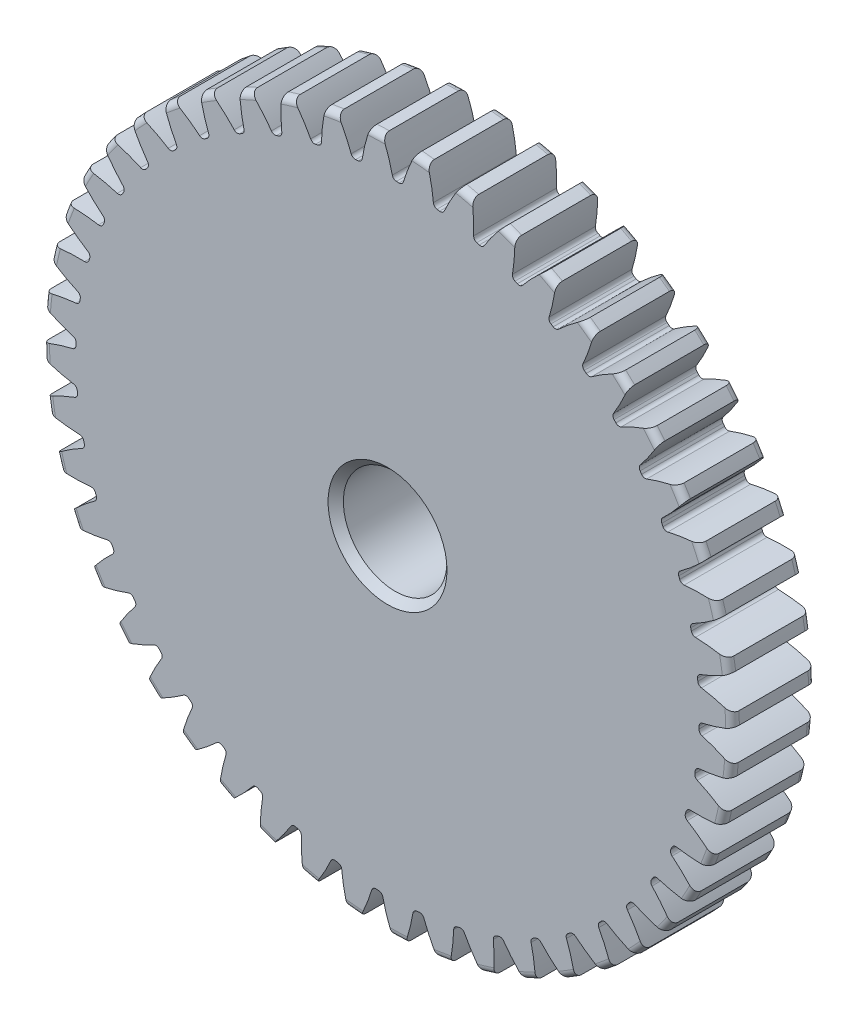
SolidWorks part; units mm, degrees
ref_plane "Front" through (0, 0, 0) normal (0, 0, 1) x (1, 0, 0)
ref_plane "Top" through (0, 0, 0) normal (0, 1, 0) x (1, 0, 0)
ref_plane "Right" through (0, 0, 0) normal (1, 0, 0) x (0, 0, -1)
sketch "Sketch1" plane through (0, 0, 0) normal (0, 0, 1) x (1, 0, 0)
  line L0 (-609.6, 0) -> (609.6, 0) construction
  circle A0 centre (0, 0) radius 26.416
  circle A1 centre (0, 0) radius 25.4 construction
  circle A3 centre (0, 0) radius 24.1755 construction
  dimension "D1" = 1.2245
  dimension "D2" = 2.2405
  dimension "D3" = 1.016
extrude "Boss-Extrude1" add sketch "Sketch1" against normal blind 6.35
sketch "Sketch2" plane through (0, 0, 0) normal (1, 0, 0) x (0, 0, -1)
  line L0 (6.35, 0) -> (14.224, 0)
  line L1 (6.35, 0) -> (6.35, 11.7078)
  line L2 (6.35, 11.7078) -> (14.224, 11.7078)
  line L3 (14.224, 11.7078) -> (14.224, 0)
  point P5 (14.224, -11.7078)
  point P6 (0, -26.416)
  point P7 (6.35, -26.416)
  point P9 (0, 26.416)
revolve "Revolve1" add sketch "Sketch2" angle 360 mid plane about L0
fillet "Fillet2" radius 0.5283 3 edges at (26.416, 0, -6.35) (26.416, 0, 0) (11.7078, 0, -6.35)
sketch "Sketch3" plane through (0, 0, 0) normal (0, 0, 1) x (1, 0, 0)
  line L0 (0, 0) -> (0, 26.416) construction
  line L1 (-8.1634, 22.4288) -> (0, 25.4)
  line L2 (-9.5921, 25.4) -> (9.5921, 25.4) construction
  line L3 (-9.0136, 22.1193) -> (9.0136, 28.6807) construction
  line L4 (-8.1634, 22.4288) -> (0, 0) construction
  line L5 (-19.9021, 13.1757) -> (0, 0) construction
  line L6 (-19.9021, 13.1757) -> (-6.7143, 33.096) construction
  line L7 (-5.6706, 23.1848) -> (0, 0) construction
  line L8 (-5.6706, 23.1848) -> (0.2364, 24.6296) construction
  arc A0 (-8.1634, 22.4288) -> (-19.9021, 13.1757) centre (0, 0) ccw
  circle A1 centre (0, 0) radius 25.4 construction
  circle A2 centre (0, 0) radius 23.8682 construction
  arc A3 (-8.1634, 22.4288) -> (-5.6706, 23.1848) centre (0, 0) cw
  circle A4 centre (0, 0) radius 26.416 construction
  point P6 (0, 25.4)
  dimension "D1" = 8.6873
  dimension "D3" = 23.8901
  dimension "D5" = 6.0811
  dimension "D2" = 15.2028
  dimension "D4" = 2.6062
sketch "Sketch4" plane through (0, 0, 0) normal (0, 0, 1) x (1, 0, 0)
  line L0 (0, 0) -> (0.8306, 25.3728) construction
  line L2 (0, 25.4) -> (1.6612, 25.3456) construction
  line L4 (0.4216, 23.8645) -> (0, 0) construction
  line L6 (-19.9021, 13.1757) -> (-6.7143, 33.096) construction
  line L7 (-19.9021, 13.1757) -> (-6.7143, 33.096) construction
  arc A0 (1.1401, 23.8409) -> (0.4216, 23.8645) centre (0, 0) ccw
  arc A1 (0, 25.4) -> (1.6612, 25.3456) centre (0, 0) cw construction
  circle A2 centre (0, 0) radius 25.4 construction
  circle A3 centre (0, 0) radius 23.8682 construction
  arc A5 (8.8645, 32.586) -> (-6.7143, 33.096) centre (0, 0) ccw
  spline S0 degree 2 poles (-6.7143, 33.096) (-0.803, 29.6485) (0.4216, 23.8645) knots 0 0 0 1 1 1
  spline S1 degree 2 poles (8.8645, 32.586) (2.7403, 29.5325) (1.1401, 23.8409) knots 0 0 0 1 1 1
  dimension "D1" = 1.6624
extrude "Cut-Extrude1" cut sketch "Sketch4" against normal through all
fillet "Fillet1" radius 0.3325 2 edges at (1.1401, 23.8409, -3.175) (0.4216, 23.8645, -3.175)
pattern_circular "CirPattern1" count 48 over 360 about axis through (0, 0, -6.35) along (0, 0, 1) of "Cut-Extrude1", "Fillet1"
sketch "Sketch5" plane through (0, 0, 0) normal (0, 0, 1) x (1, 0, 0)
  circle A0 centre (0, 0) radius 3.9688
  circle A1 centre (0, 0) radius 3.9688 construction
  dimension "Bore Min" = 7.9375
  dimension "Bore Max" = 7.9375
extrude "Cut-Extrude2" cut sketch "Sketch5" against normal through all
chamfer "Chamfer1" distance 0.5854 angle 45 3 edges at (11.7078, 0, -14.224) (3.9688, 0, 0) (3.9688, 0, -14.224)
sketch "Pitch Dia" plane through (0, 0, 0) normal (0, 0, 1) x (1, 0, 0)
  circle A0 centre (0, 0) radius 25.4 construction
  circle A1 centre (0, 0) radius 25.4 construction
sketch "Sketch6" plane through (0, 0, 0) normal (0, 0, 1) x (1, 0, 0)
  line L0 (-1.3337, 26.3823) -> (-0.3947, 26.4131)
  line L1 (-0.8642, 26.3977) -> (-0.7719, 23.5785) construction
  arc A0 (-2.2394, 23.7629) -> (-1.9424, 24.0403) centre (-2.2706, 24.0939) ccw construction
  arc A1 (-2.2394, 23.7629) -> (-2.4396, 23.7432) centre (0, 0) ccw construction
  arc A2 (0.366, 24.1159) -> (0.6804, 23.8585) centre (0.6899, 24.1908) ccw construction
  arc A3 (0.8815, 23.8519) -> (0.6804, 23.8585) centre (0, 0) ccw construction
  circle A4 centre (0, 0) radius 26.416 construction
  parabola Q2 (-1.5162, 25.8432) -> (-1.3337, 26.3823) focus (4.6524, 24.5229) apex (-1.1149, 26.9412) construction
  parabola Q3 (-1.9424, 24.0403) -> (-1.5162, 25.8432) focus (4.6524, 24.5229) apex (-1.1149, 26.9412) construction
  parabola Q4 (-1.9424, 24.0403) -> (-1.5162, 25.8432) focus (4.6524, 24.5229) apex (-1.1149, 26.9412) construction
  parabola Q5 (-1.9424, 24.0403) -> (-1.5162, 25.8432) focus (4.6524, 24.5229) apex (-1.1149, 26.9412) construction
  parabola Q6 (-1.9424, 24.0403) -> (-1.5162, 25.8432) focus (4.6524, 24.5229) apex (-1.1149, 26.9412) construction
  spline S0 degree 3 poles (-1.3337, 26.3823) (-1.3986, 26.204) (-1.4881, 25.9395) (-1.6086, 25.5407) (-1.6684, 25.3219) (-1.7024, 25.1889) knots 0 0 0 0 0.455486 0.670301 1 1 1 1
  spline S1 degree 3 poles (-1.7024, 25.1889) (-1.7636, 24.906) (-1.8284, 24.543) (-1.924, 24.1631) (-1.9413, 24.0397) (-1.9588, 23.9693) (-1.9959, 23.9009) (-2.0556, 23.8348) (-2.1669, 23.7641) (-2.2735, 23.7587) (-2.3395, 23.7533) knots 0 0 0 0 0.50758 0.647219 0.68628 0.726157 0.773713 0.821128 0.881401 1 1 1 1
  spline S2 degree 3 poles (-0.3947, 26.4131) (-0.3182, 26.2394) (-0.2116, 25.9813) (-0.0653, 25.5913) (0.0087, 25.3768) (0.0514, 25.2463) knots 0 0 0 0 0.455486 0.670301 1 1 1 1
  spline S3 degree 3 poles (0.0514, 25.2463) (0.1141, 25.0361) (0.1742, 24.7693) (0.2761, 24.4493) (0.321, 24.282) (0.3561, 24.146) (0.3832, 24.0582) (0.4097, 24.0095) (0.4401, 23.969) (0.4848, 23.9267) (0.5415, 23.8901) (0.6424, 23.8533) (0.7263, 23.8582) (0.7809, 23.8554) knots 0 0 0 0 0.384807 0.478666 0.588978 0.688379 0.725395 0.749588 0.785292 0.813657 0.857185 0.902571 1 1 1 1
equation "\"D1@Boss-Extrude1\" = \"Face Wd@Sketch2\""
equation "\"D2@Sketch3\" = \"D1@Sketch3\"*1.75"
equation "\"D3@Sketch3\" = \"D1@Sketch3\"+\"D2@Sketch3\""
equation "\"D4@Sketch3\" = \"D1@Sketch3\"*.3"
equation "\"D5@Sketch3\" = \"D1@Sketch3\"-\"D4@Sketch3\""
equation "\"D1@Sketch4\" = 1.5708/(\"Number of Teeth@Sketch1\"/\"Ptich Dia@Sketch1\")"
equation "\"D1@Chamfer1\" = \"B Hub Dia@Sketch2\"*.025"
equation "\"D1@CirPattern1\" = \"Number of Teeth@Sketch1\""
equation "\"D1@Fillet1\" = \"D1@Sketch4\"*.2"
equation "\"D1@Fillet2\" = \"OD@Sketch1\"*.01"
equation "\"D1@Sketch1\" = 1.157/(\"Number of Teeth@Sketch1\"/\"Ptich Dia@Sketch1\")"
